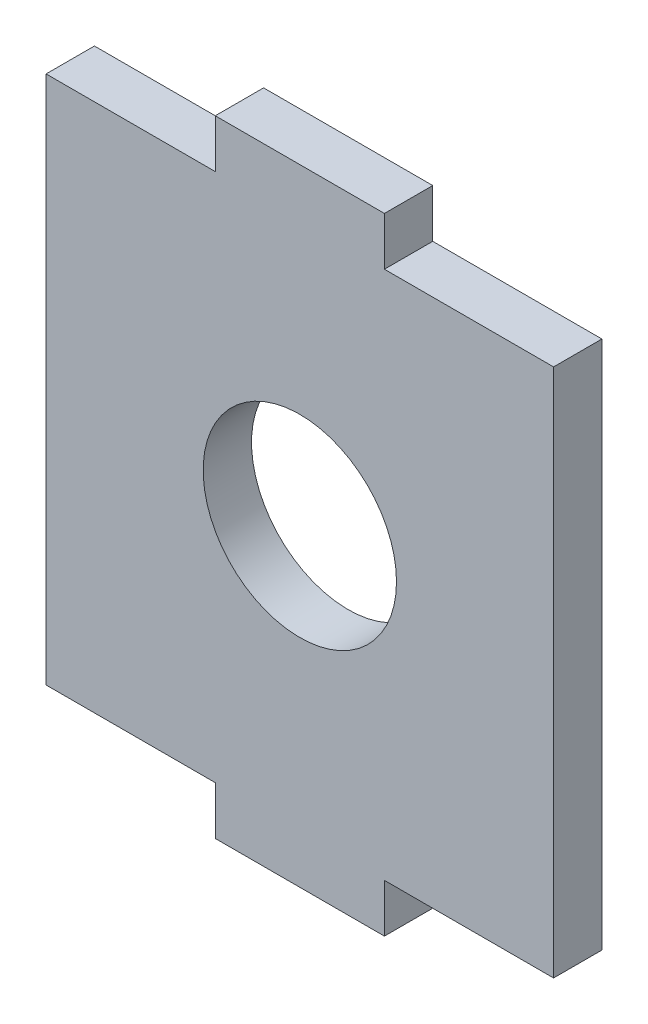
SolidWorks part; units mm, degrees
ref_plane "Front Plane" through (0, 0, 0) normal (0, 0, 1) x (1, 0, 0)
ref_plane "Top Plane" through (0, 0, 0) normal (0, 1, 0) x (1, 0, 0)
ref_plane "Right Plane" through (0, 0, 0) normal (1, 0, 0) x (0, 0, -1)
sketch "Sketch1" plane through (0, 0, 0) normal (0, 0, 1) x (1, 0, 0)
  line L0 (3.5, 10.95) -> (10.5, 10.95)
  line L1 (-10.5, -10.95) -> (-3.5, -10.95)
  line L2 (-10.5, -10.95) -> (-10.5, 10.95)
  line L3 (-10.5, 10.95) -> (-3.5, 10.95)
  line L4 (10.5, -10.95) -> (10.5, 10.95)
  line L5 (-10.5, -10.95) -> (10.5, 10.95) construction
  line L6 (-10.5, 10.95) -> (10.5, -10.95) construction
  line L8 (-3.5, 10.95) -> (-3.5, 12.95)
  line L9 (-3.5, 12.95) -> (3.5, 12.95)
  line L10 (3.5, 10.95) -> (3.5, 12.95)
  line L12 (-3.5, -10.95) -> (-3.5, -12.95)
  line L13 (-3.5, -12.95) -> (3.5, -12.95)
  line L14 (3.5, -10.95) -> (3.5, -12.95)
  line L15 (3.5, -10.95) -> (10.5, -10.95)
  circle A0 centre (0, 0) radius 4
  point P0 (0, 0)
  point P16 (0, -12.95)
  point P17 (0, 12.95)
  dimension "D2" = 8
  dimension "D1" = 21
  dimension "D3" = 21.9
  dimension "D4" = 7
  dimension "D5" = 2
extrude "Boss-Extrude1" add sketch "Sketch1" along normal blind 2
